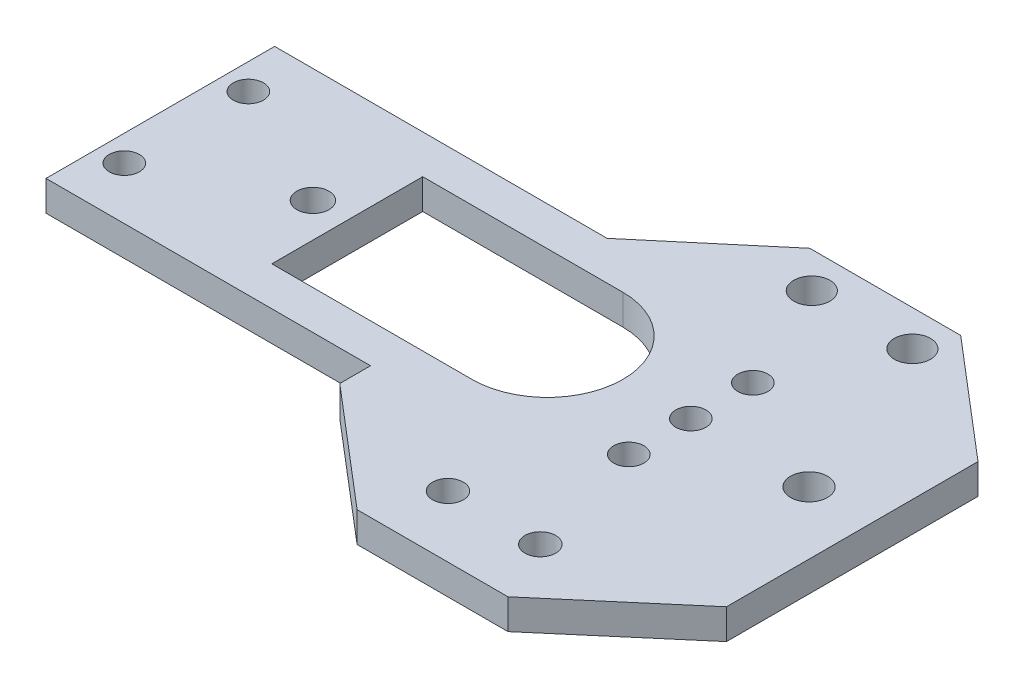
SolidWorks part; units mm, degrees
ref_plane "Alzado" through (0, 0, 0) normal (0, 0, 1) x (1, 0, 0)
ref_plane "Planta" through (0, 0, 0) normal (0, 1, 0) x (1, 0, 0)
ref_plane "Vista lateral" through (0, 0, 0) normal (1, 0, 0) x (0, 0, -1)
sketch "Croquis1" plane through (0, 0, 0) normal (0, 1, 0) x (1, 0, 0)
  line L0 (-26.5149, -10.5826) -> (-26.5149, -7.5272)
  line L1 (-14.7949, 24.4174) -> (0.2051, 24.4174)
  line L2 (-26.5149, -10.5826) -> (-14.7949, -20.5826)
  line L3 (-14.7949, -20.5826) -> (0.2051, -20.5826)
  line L4 (11.9251, 14.4174) -> (11.9251, -10.5826)
  line L5 (-7.2949, -20.5826) -> (-7.2949, 24.4174) construction
  line L6 (-26.5149, -7.5272) -> (-40.887, -7.5272)
  line L7 (11.9251, -10.5826) -> (0.2051, -20.5826)
  line L8 (-25.725, 15.2001) -> (-14.7949, 24.4174)
  line L9 (0.2051, 24.4174) -> (11.9251, 14.4174)
  line L10 (-14.7949, -20.5826) -> (-14.7949, 24.4174) construction
  line L11 (0.2051, -20.5826) -> (0.2051, 24.4174) construction
  line L12 (-14.7949, -2.3239) -> (0.2051, -2.3239) construction
  line L13 (11.9251, -10.5826) -> (-26.5149, -10.5826) construction
  line L14 (11.9251, 14.4174) -> (-27.2565, 14.4174) construction
  line L15 (-41.4058, 15.2001) -> (-25.725, 15.2001)
  line L16 (-11.8849, -14.4576) -> (-2.7049, -14.4576) construction
  line L17 (-20.2949, 3.8424) -> (5.7051, 3.8424) construction
  line L18 (-52.2565, 3.8424) -> (-52.2565, 28.8425) construction
  line L19 (-40.1956, 11.3424) -> (-20.2949, 11.3424)
  line L20 (-40.1956, 11.3424) -> (-40.1956, -3.6576)
  line L21 (-40.1956, -3.6576) -> (-20.2949, -3.6576)
  line L22 (-20.2949, 3.8424) -> (-52.2565, 3.8424) construction
  line L23 (-27.2565, 14.4174) -> (-27.2565, 26.4393) construction
  line L24 (-41.4058, 15.2001) -> (-58.7725, 15.2001)
  line L25 (-58.7725, 15.2001) -> (-58.7725, -7.5272)
  line L26 (-58.7725, -7.5272) -> (-40.887, -7.5272)
  line L27 (-6.0449, 10.0086) -> (-6.0449, -2.3239) construction
  line L28 (-14.7949, 10.0086) -> (0.2051, 10.0086) construction
  line L29 (-14.7949, 10.0086) -> (-58.7725, 10.0086) construction
  line L30 (-14.7949, -2.3239) -> (-58.7725, -2.3239) construction
  line L31 (-56.1949, 15.2001) -> (-56.1949, -7.5272) construction
  line L32 (-25.725, 15.2001) -> (-25.725, 14.4174) construction
  arc A0 (-41.4058, 15.2001) -> (-40.887, -7.5272) centre (-40.887, 3.8424) ccw construction
  circle A1 centre (-11.8849, -14.4576) radius 1.53
  circle A2 centre (-2.7049, -14.4576) radius 1.53
  arc A3 (-20.2949, -3.6576) -> (-20.2949, 11.3424) centre (-20.2949, 3.8424) ccw
  circle A4 centre (5.7051, 3.8424) radius 1.8379
  circle A5 centre (-43.6105, 3.8424) radius 1.5973
  circle A6 centre (-6.0449, 3.8424) radius 1.5
  circle A7 centre (-6.0449, 10.0086) radius 1.5
  circle A8 centre (-6.0449, -2.3239) radius 1.5
  circle A9 centre (-20.2949, 3.8424) radius 7.5 construction
  circle A10 centre (-56.1949, 10.0086) radius 1.5
  circle A11 centre (-56.1949, -2.3239) radius 1.5
  point P0 (0, 0)
  point P16 (0, 0)
  dimension "D12" = 3
  dimension "D13" = 15
  dimension "D10" = 3.06
  dimension "D1" = 15
  dimension "D2" = 10
  dimension "D3" = 45
  dimension "D4" = 10
  dimension "D5" = 6.125
  dimension "D6" = 26
  dimension "D7" = 18.3
  dimension "D8" = 9.18
  dimension "D9" = 25
  dimension "D11" = 14.25
  dimension "D14" = 48.9
extrude "Saliente-Extruir1" add sketch "Croquis1" along normal blind 3
sketch "Croquis2" plane through (0, 3, 0) normal (0, 1, 0) x (1, 0, 0)
  line L0 (-13.6286, 20.8624) -> (0, 20.8624) construction
  circle A0 centre (-11.0392, 20.8624) radius 1.8
  circle A1 centre (-1.0392, 20.8624) radius 1.8
  dimension "D1" = 3.6
  dimension "D2" = 10
extrude "Cortar-Extruir1" cut sketch "Croquis2" against normal blind 10
